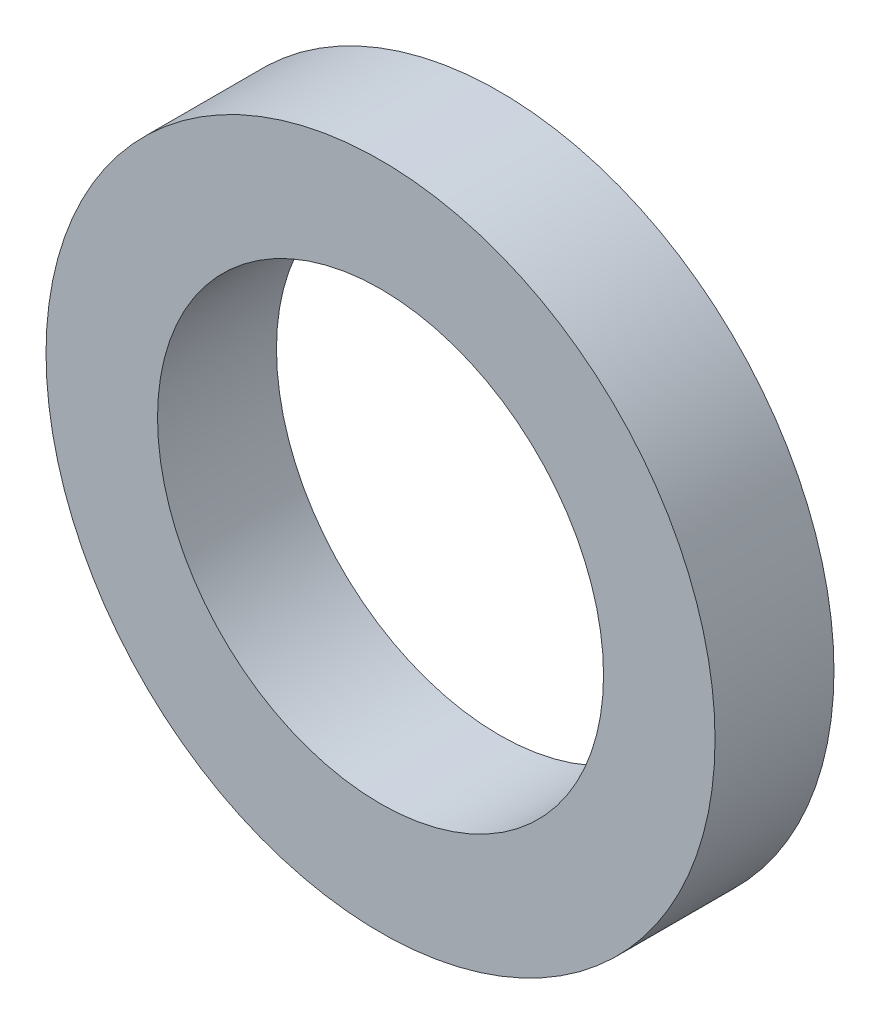
SolidWorks part; units mm, degrees
ref_plane "Front" through (0, 0, 0) normal (0, 0, 1) x (1, 0, 0)
ref_plane "Top" through (0, 0, 0) normal (0, 1, 0) x (1, 0, 0)
ref_plane "Right" through (0, 0, 0) normal (1, 0, 0) x (0, 0, -1)
sketch "草图1" plane through (0, 0, 0) normal (0, 0, 1) x (1, 0, 0)
  circle A0 centre (0, 0) radius 4.5
  circle A1 centre (0, 0) radius 3
  dimension "D1" = 9
  dimension "D2" = 6
extrude "凸台-拉伸1" add sketch "草图1" along normal blind 1.6
